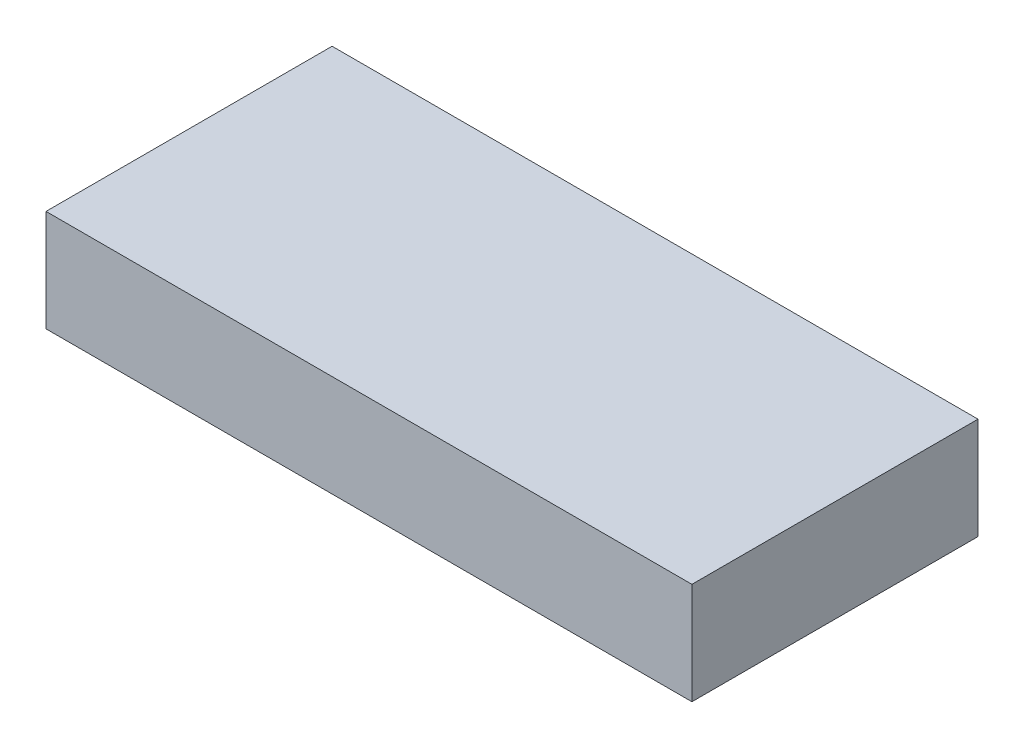
SolidWorks part; units mm, degrees
ref_plane "Front Plane" through (0, 0, 0) normal (0, 0, 1) x (1, 0, 0)
ref_plane "Top Plane" through (0, 0, 0) normal (0, 1, 0) x (1, 0, 0)
ref_plane "Right Plane" through (0, 0, 0) normal (1, 0, 0) x (0, 0, -1)
sketch "Sketch1" plane through (0, 0, 0) normal (0, 1, 0) x (1, 0, 0)
  line L1 (-15.24, -6.75) -> (15.24, -6.75)
  line L2 (-15.24, -6.75) -> (-15.24, 6.75)
  line L3 (-15.24, 6.75) -> (15.24, 6.75)
  line L4 (15.24, -6.75) -> (15.24, 6.75)
  line L5 (-15.24, -6.75) -> (15.24, 6.75) construction
  line L6 (-15.24, 6.75) -> (15.24, -6.75) construction
  point P0 (0, 0)
  dimension "D1" = 13.5
  dimension "D2" = 30.48
extrude "Boss-Extrude1" add sketch "Sketch1" along normal blind 4.8
